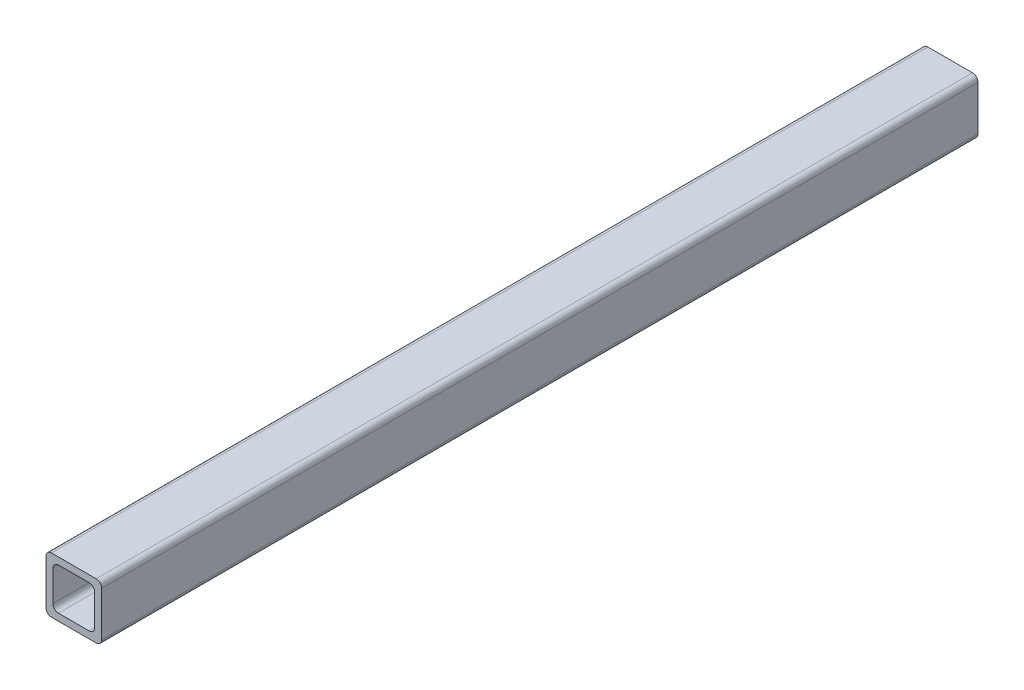
SolidWorks part; units mm, degrees
ref_plane "Alzado" through (0, 0, 0) normal (0, 0, 1) x (1, 0, 0)
ref_plane "Planta" through (0, 0, 0) normal (0, 1, 0) x (1, 0, 0)
ref_plane "Vista lateral" through (0, 0, 0) normal (1, 0, 0) x (0, 0, -1)
sketch "Croquis1" plane through (0, 0, 0) normal (0, 0, 1) x (1, 0, 0)
  line L1 (-7.025, -9.525) -> (7.025, -9.525)
  line L2 (-9.525, -7.025) -> (-9.525, 7.025)
  line L3 (-7.025, 9.525) -> (7.025, 9.525)
  line L4 (9.525, -7.025) -> (9.525, 7.025)
  line L5 (-9.525, -9.525) -> (9.525, 9.525) construction
  line L6 (-9.525, 9.525) -> (9.525, -9.525) construction
  line L7 (-10.2, -12.7) -> (10.2, -12.7)
  line L8 (-12.7, -10.2) -> (-12.7, 10.2)
  line L9 (-10.2, 12.7) -> (10.2, 12.7)
  line L10 (12.7, -10.2) -> (12.7, 10.2)
  line L11 (-12.7, -12.7) -> (12.7, 12.7) construction
  line L12 (-12.7, 12.7) -> (12.7, -12.7) construction
  arc A0 (-7.025, -9.525) -> (-9.525, -7.025) centre (-7.025, -7.025) cw
  arc A1 (7.025, -9.525) -> (9.525, -7.025) centre (7.025, -7.025) ccw
  arc A2 (9.525, 7.025) -> (7.025, 9.525) centre (7.025, 7.025) ccw
  arc A3 (12.7, -10.2) -> (10.2, -12.7) centre (10.2, -10.2) cw
  arc A4 (-10.2, -12.7) -> (-12.7, -10.2) centre (-10.2, -10.2) cw
  arc A5 (12.7, 10.2) -> (10.2, 12.7) centre (10.2, 10.2) ccw
  arc A6 (-9.525, 7.025) -> (-7.025, 9.525) centre (-7.025, 7.025) cw
  arc A7 (-10.2, 12.7) -> (-12.7, 10.2) centre (-10.2, 10.2) ccw
  point P0 (0, 0)
  point P6 (0, 0)
  dimension "D3" = 2.5
  dimension "D1" = 25.4
  dimension "D2" = 3.175
extrude "Saliente-Extruir1" add sketch "Croquis1" along normal blind 400
